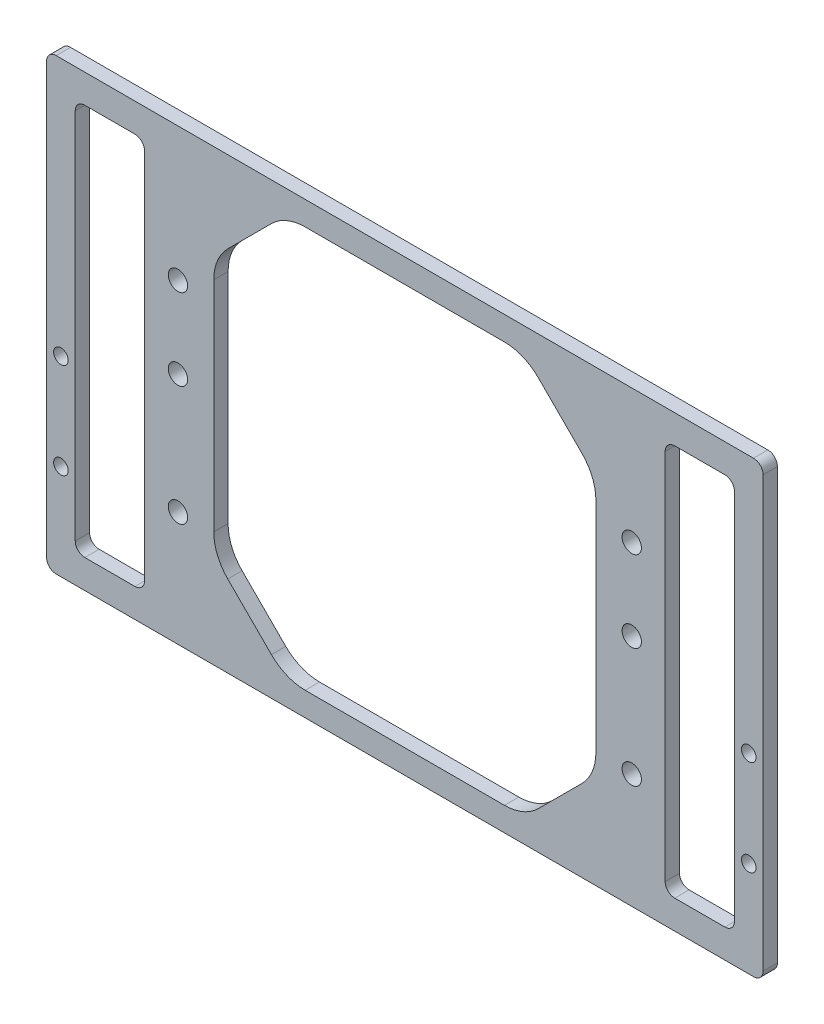
SolidWorks part; units mm, degrees
material "Thornel Mat VMA"
ref_plane "前视基准面" through (0, 0, 0) normal (0, 0, 1) x (1, 0, 0)
ref_plane "上视基准面" through (0, 0, 0) normal (0, 1, 0) x (1, 0, 0)
ref_plane "右视基准面" through (0, 0, 0) normal (1, 0, 0) x (0, 0, -1)
other "Configuration Table"
sketch "草图1" plane through (0, 0, 0) normal (0, 0, 1) x (1, 0, 0)
  line L0 (-47.5, 0) -> (47.5, 0) construction
  line L1 (-47.5, 17) -> (-47.5, 0) construction
  line L2 (-47.5, 0) -> (-47.5, -25) construction
  line L3 (0, 0) -> (0, -50000) construction
  line L5 (75, -49) -> (-75, -49)
  line L6 (75, -49) -> (75, 45)
  line L7 (75, 45) -> (-75, 45)
  line L8 (-75, -49) -> (-75, 45)
  line L9 (75, -49) -> (-75, 45) construction
  line L10 (75, 45) -> (-75, -49) construction
  line L11 (-40, -44) -> (40, -44)
  line L12 (-40, -44) -> (-40, 40)
  line L13 (-40, 40) -> (40, 40)
  line L14 (40, -44) -> (40, 40)
  line L15 (-40, -44) -> (40, 40) construction
  line L16 (-40, 40) -> (40, -44) construction
  circle A0 centre (-47.5, 0) radius 2.025
  circle A1 centre (-47.5, 17) radius 2.025
  circle A2 centre (-47.5, -25) radius 2.025
  circle A3 centre (47.5, -25) radius 2.025
  circle A4 centre (47.5, 17) radius 2.025
  circle A5 centre (47.5, 0) radius 2.025
  point P3 (0, -2)
  point P4 (0, 0)
  point P21 (0, -2)
  dimension "D1" = 17
  dimension "D2" = 25
  dimension "D3" = 4.05
  dimension "D4" = 47.5
  dimension "D5" = 24
  dimension "D7" = 94
  dimension "D6" = 150
  dimension "D8" = 5
  dimension "D9" = 7.5
extrude "凸台-拉伸1" add sketch "草图1" along normal blind 3
chamfer "倒角1" distance 15 angle 45 4 edges at (40, -44, 1.5) (40, 40, 1.5) (-40, 40, 1.5) (-40, -44, 1.5)
fillet "圆角1" radius 10 8 edges at (-25, 40, 1.5) (-40, 25, 1.5) (-40, -29, 1.5) (-25, -44, 1.5) (40, -29, 1.5) (40, 25, 1.5) (25, 40, 1.5) (25, -44, 1.5)
sketch "草图2" plane through (0, 0, 3) normal (0, 0, 1) x (1, 0, 0)
  line L0 (-67.5, -2) -> (-50067.5, -2) construction
  line L1 (-69, 39) -> (-54.5, 39)
  line L2 (-69, 39) -> (-69, -43)
  line L3 (-69, -43) -> (-54.5, -43)
  line L4 (-54.5, 39) -> (-54.5, -43)
  line L5 (69, 39) -> (54.5, 39)
  line L6 (69, 39) -> (69, -43)
  line L7 (69, -43) -> (54.5, -43)
  line L8 (54.5, 39) -> (54.5, -43)
  line L9 (-75, 45) -> (-75, -49) construction
  line L10 (75, 45) -> (-75, 45) construction
  line L11 (0, 0) -> (0, -50000) construction
  circle A0 centre (-47.5, 0) radius 2.025 construction
  point P12 (-75, -2)
  dimension "D1" = 6
  dimension "D2" = 6
  dimension "D3" = 7
extrude "切除-拉伸1" cut sketch "草图2" against normal blind 10
fillet "圆角2" radius 2 12 edges at (-75, 45, 1.5) (75, -49, 1.5) (-75, -49, 1.5) (69, 39, 1.5) (54.5, 39, 1.5) (54.5, -43, 1.5) (69, -43, 1.5) (-69, -43, 1.5) (-54.5, -43, 1.5) (-54.5, 39, 1.5) (-69, 39, 1.5) (75, 45, 1.5)
sketch "草图3" plane through (0, 0, 3) normal (0, 0, 1) x (1, 0, 0)
  line L0 (0, 0) -> (0, -50000) construction
  line L1 (72, -9) -> (72, -29) construction
  line L3 (75, -47) -> (75, 43) construction
  line L4 (-73, -49) -> (73, -49) construction
  line L5 (-72, -9) -> (-72, -29) construction
  circle A0 centre (72, -9) radius 1.525
  circle A1 centre (72, -29) radius 1.525
  circle A2 centre (-72, -29) radius 1.525
  circle A3 centre (-72, -9) radius 1.525
  dimension "D4" = 3.05
  dimension "D1" = 20
  dimension "D2" = 3
  dimension "D3" = 20
extrude "切除-拉伸2" cut sketch "草图3" against normal blind 10
